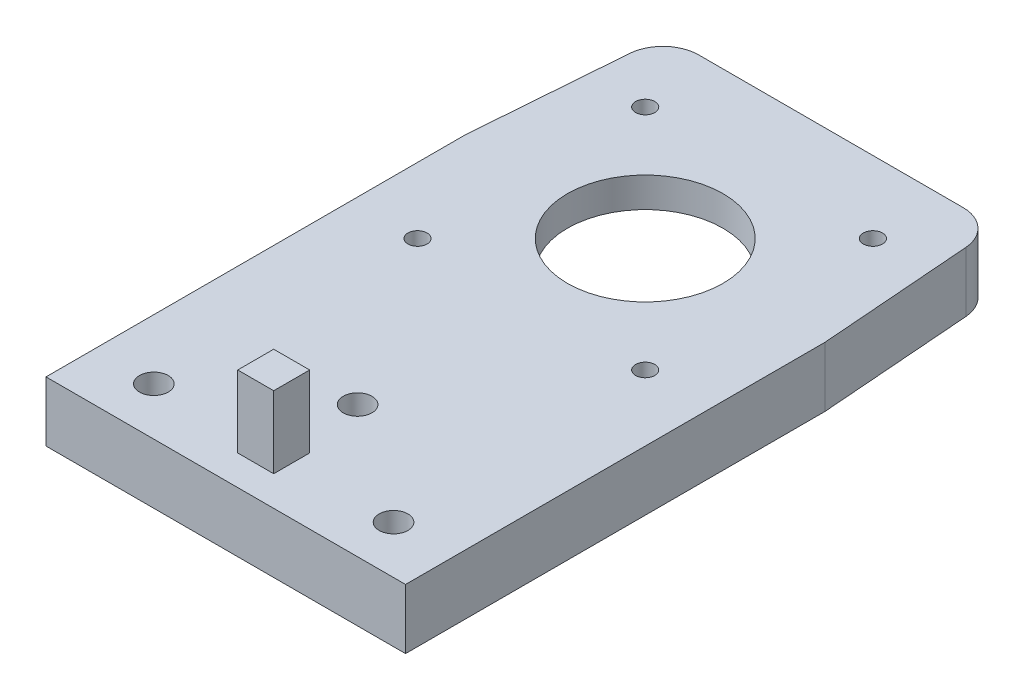
SolidWorks part; units mm, degrees
material "7075-T6 (SN)"
ref_plane "Front Plane" through (0, 0, 0) normal (0, 0, 1) x (1, 0, 0)
ref_plane "Top Plane" through (0, 0, 0) normal (0, 1, 0) x (1, 0, 0)
ref_plane "Right Plane" through (0, 0, 0) normal (1, 0, 0) x (0, 0, -1)
sketch "Sketch1" plane through (0, 0, 0) normal (0, 1, 0) x (1, 0, 0)
  line L0 (-15, 0) -> (15, 0)
  line L1 (-15, 0) -> (-15, 35)
  line L2 (15, 0) -> (15, 35)
  line L3 (-15, 35) -> (-13.8077, 50.5)
  line L4 (-13.8077, 50.5) -> (13.8077, 50.5)
  line L5 (13.8077, 50.5) -> (15, 35)
  line L6 (-14, 48) -> (14, 48) construction
  point P4 (0, 50.5)
  dimension "D1" = 35
  dimension "D2" = 30
  dimension "D3" = 15.5
  dimension "D4" = 1
  dimension "D5" = 2.5
extrude "Boss-Extrude1" add sketch "Sketch1" along normal blind 5
sketch "Sketch2" plane through (0, 5, 0) normal (0, 1, 0) x (1, 0, 0)
  circle A0 centre (0, 35) radius 6.4897
  dimension "D1" = 12.9794
extrude "Cut-Extrude1" cut sketch "Sketch2" against normal up to next
sketch "Sketch3" plane through (0, 5, 0) normal (0, 1, 0) x (1, 0, 0)
  line L0 (-15, 0) -> (15, 0) construction
  line L1 (-1.5, 5.5) -> (1.5, 5.5)
  line L2 (-1.5, 5.5) -> (-1.5, 2.5)
  line L3 (-1.5, 2.5) -> (1.5, 2.5)
  line L4 (1.5, 5.5) -> (1.5, 2.5)
  point P4 (0, 2.5)
  point P6 (1.5, 4)
  dimension "D1" = 4
  dimension "D2" = 3
extrude "Boss-Extrude2" add sketch "Sketch3" along normal blind 6
hole_wizard "CSK for M2 Countersunk Flat Head Screw1" positions "Sketch4" profile "Sketch5" countersink size "M2" standard "DIN"
sketch "Sketch4" plane through (0, 0, 0) normal (0, -1, 0) x (-1, 0, 0)
  line L0 (15, 0) -> (-15, 0) construction
  point P0 (-10, 4)
  point P2 (10, 4)
  point P4 (0, 11)
  dimension "D1" = 4
  dimension "D2" = 10
  dimension "D3" = 10
  dimension "D4" = 11
sketch "Sketch5" plane through (10, 0, -4) normal (1, 0, 0) x (0, 0, -1)
  line L0 (0, 0) -> (0, 5.921)
  line L1 (0, 5.921) -> (1.2, 5.2)
  line L2 (1.2, 5.2) -> (1.2, 1.5)
  line L3 (1.2, 1.5) -> (2.7, 0)
  line L5 (2.7, 0) -> (0, 0)
  line L6 (-1.2, 1.5) -> (-2.7, 0) construction
  line L10 (0, 5.921) -> (-1.2, 5.2) construction
  line L11 (0, -6.35) -> (0, 107.95) construction
  dimension "Hole Dia." = 2.4
  dimension "Hole Depth" = 5.2
  dimension "Near C'Sink Dia." = 5.4
  dimension "Near C'Sink Angle" = 90
  dimension "Drill Angle" = 118
sketch "Sketch6" plane through (0, 0, 0) normal (0, -1, 0) x (1, 0, 0)
  line L1 (-10.5, -48) -> (10.5, -48)
  line L2 (-13, -45.5) -> (-13, -24.5)
  line L3 (-10.5, -22) -> (10.5, -22)
  line L4 (13, -45.5) -> (13, -24.5)
  line L5 (-13, -48) -> (13, -22) construction
  line L6 (-13, -22) -> (13, -48) construction
  arc A0 (-10.5, -48) -> (-13, -45.5) centre (-10.5, -45.5) cw
  arc A1 (10.5, -48) -> (13, -45.5) centre (10.5, -45.5) ccw
  arc A2 (10.5, -22) -> (13, -24.5) centre (10.5, -24.5) cw
  arc A3 (-13, -24.5) -> (-10.5, -22) centre (-10.5, -24.5) cw
  point P0 (0, -35)
  dimension "D2" = 2.5
  dimension "D1" = 26
extrude "Cut-Extrude2" cut sketch "Sketch6" against normal blind 2.5
fillet "Fillet1" radius 3 2 edges at (13.8077, 2.5, -50.5) (-13.8077, 2.5, -50.5)
hole_wizard "M2 Tapped Hole1" positions "Sketch7" profile "Sketch8" tap size "M2" standard "DIN" end condition up to next
sketch "Sketch7" plane through (0, 2.5, 0) normal (0, -1, 0) x (-1, 0, 0)
  circle A0 centre (0, 35) radius 6.4897 construction
  point P0 (9.5, 25.5)
  point P2 (9.5, 44.5)
  point P4 (-9.5, 44.5)
  point P6 (-9.5, 25.5)
  dimension "D1" = 19
  dimension "D2" = 19
  dimension "D3" = 9.5
  dimension "D4" = 9.5
sketch "Sketch8" plane through (-9.5, 2.5, -25.5) normal (1, 0, 0) x (0, 0, -1)
  line L0 (0, 0) -> (0, 2.5)
  line L1 (0, 2.5) -> (0.8, 2.5)
  line L2 (0.8, 2.5) -> (0.8, 0)
  line L5 (0.8, 0) -> (0, 0)
  line L11 (0, -6.35) -> (0, 107.95) construction
  dimension "Thru Tap Drill Dia." = 1.6
  dimension "Thru Tap Drill Depth" = 2.5
cosmetic thread "Hole Thread1" parameters "D2"=2
cosmetic thread "Hole Thread2" parameters "D2"=2
cosmetic thread "Hole Thread3" parameters "D2"=2
cosmetic thread "Hole Thread4" parameters "D2"=2
